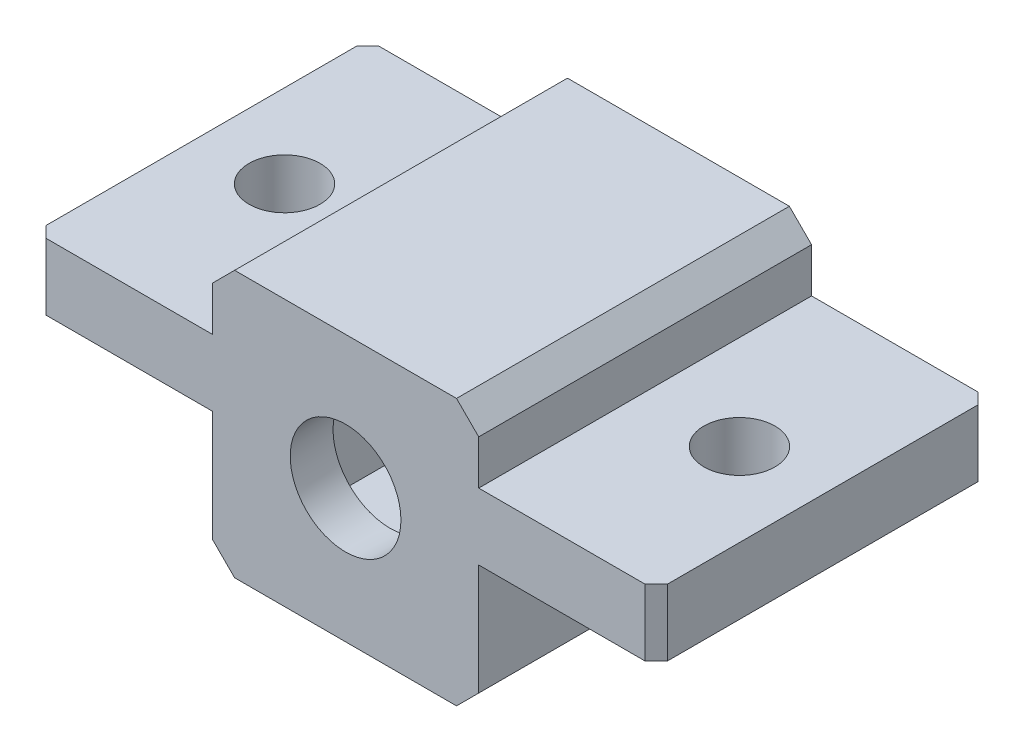
SolidWorks part; units mm, degrees
ref_plane "Plan de face" through (0, 0, 0) normal (0, 0, 1) x (1, 0, 0)
ref_plane "Plan de dessus" through (0, 0, 0) normal (0, 1, 0) x (1, 0, 0)
ref_plane "Plan de droite" through (0, 0, 0) normal (1, 0, 0) x (0, 0, -1)
sketch "Esquisse1" plane through (0, 0, 0) normal (0, 0, 1) x (1, 0, 0)
  line L1 (-34.6304, 29.1827) -> (-22.6304, 29.1827)
  line L2 (-34.6304, 29.1827) -> (-34.6304, 17.1827)
  line L3 (-34.6304, 17.1827) -> (-22.6304, 17.1827)
  line L4 (-22.6304, 29.1827) -> (-22.6304, 17.1827)
  dimension "D1" = 12
  dimension "21" = 12
extrude "Boss.-Extru.1" add sketch "Esquisse1" along normal blind 15
sketch "Esquisse2" plane through (0, 0, 15) normal (0, 0, 1) x (1, 0, 0)
  line L0 (-28.6304, 29.1827) -> (-28.6304, 17.1827) construction
  line L1 (-22.6304, 29.1827) -> (-34.6304, 29.1827) construction
  line L2 (-34.6304, 17.1827) -> (-22.6304, 17.1827) construction
  line L3 (-34.6304, 23.1827) -> (-22.6304, 23.1827) construction
  line L4 (-34.6304, 29.1827) -> (-34.6304, 17.1827) construction
  line L5 (-22.6304, 17.1827) -> (-22.6304, 29.1827) construction
  circle A0 centre (-28.6304, 23.1827) radius 2.6
  dimension "D1" = 5.2
extrude "Enlèv. mat.-Extru.1" cut sketch "Esquisse2" along normal through all draft 2 from offset 3 offset against normal yes
sketch "Esquisse3" plane through (0, 0, 0) normal (0, 0, -1) x (-1, 0, 0)
  line L0 (22.6304, 17.1827) -> (22.6304, 29.1827) construction
  line L1 (24.6304, 27.1827) -> (32.6304, 27.1827)
  line L2 (24.6304, 27.1827) -> (24.6304, 19.1827)
  line L3 (24.6304, 19.1827) -> (32.6304, 19.1827)
  line L4 (32.6304, 27.1827) -> (32.6304, 19.1827)
  line L5 (22.6304, 29.1827) -> (34.6304, 29.1827) construction
  line L6 (22.6304, 23.1827) -> (34.6304, 23.1827) construction
  line L7 (34.6304, 29.1827) -> (34.6304, 17.1827) construction
  line L8 (28.6304, 29.1827) -> (28.6304, 17.1827) construction
  line L9 (34.6304, 17.1827) -> (22.6304, 17.1827) construction
  dimension "D1" = 2
  dimension "2" = 2
extrude "Enlèv. mat.-Extru.2" cut sketch "Esquisse3" against normal blind 13
chamfer "Chanfrein1" distance 1 angle 45 4 edges at (-22.6304, 17.1827, 7.5) (-22.6304, 29.1827, 7.5) (-34.6304, 29.1827, 7.5) (-34.6304, 17.1827, 7.5)
sketch "Esquisse4" plane through (-34.6304, 0, 0) normal (-1, 0, 0) x (0, 0, 1)
  line L0 (15, 28.1827) -> (15, 18.1827) construction
  line L1 (15, 23.1827) -> (0, 23.1827)
  line L2 (15, 23.1827) -> (15, 26.1827)
  line L3 (15, 26.1827) -> (0, 26.1827)
  line L4 (0, 23.1827) -> (0, 26.1827)
  line L5 (0, 29.1827) -> (15, 29.1827) construction
  dimension "D1" = 3
  dimension "D2" = 3
extrude "Boss.-Extru.2" add sketch "Esquisse4" along normal blind 8
sketch "Esquisse5" plane through (0, 23.1827, 0) normal (0, -1, 0) x (1, 0, 0)
  line L0 (-34.6304, 7.5) -> (-42.6304, 7.5) construction
  line L1 (-34.6304, 0) -> (-34.6304, 15) construction
  line L2 (-42.6304, 0) -> (-42.6304, 15) construction
  circle A0 centre (-38.8804, 7.5) radius 1.6
  dimension "D2" = 3.2
  dimension "D1" = 4.25
extrude "Enlèv. mat.-Extru.3" cut sketch "Esquisse5" against normal through all
chamfer "Chanfrein2" distance 0.5 angle 45 2 edges at (-42.6304, 24.6827, 0) (-42.6304, 24.6827, 15)
ref_plane "Plan1" through (-28.6304, 0, 0) normal (-1, 0, 0) x (0, 0, 1)
mirror "Symétrie1" about plane through (-28.6304, 0, 0) normal (-1, 0, 0) of "Chanfrein2", "Enlèv. mat.-Extru.3", "Boss.-Extru.2"
